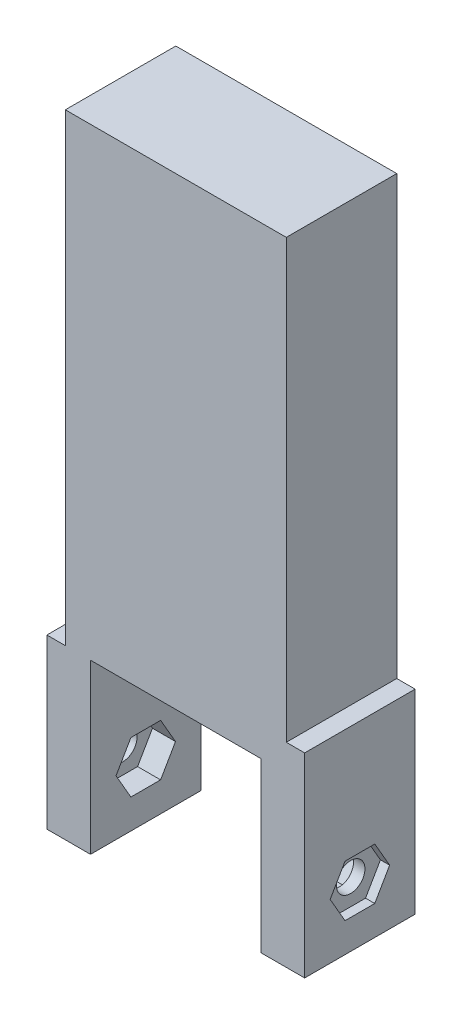
SolidWorks part; units mm, degrees
ref_plane "정면" through (0, 0, 0) normal (0, 0, 1) x (1, 0, 0)
ref_plane "윗면" through (0, 0, 0) normal (0, 1, 0) x (1, 0, 0)
ref_plane "우측면" through (0, 0, 0) normal (1, 0, 0) x (0, 0, -1)
sketch "스케치1" plane through (0, 0, 0) normal (0, 0, 1) x (1, 0, 0)
  line L0 (-11.9944, 44.775) -> (-11.9944, -5.635)
  line L1 (-11.9944, 44.775) -> (12.0056, 44.775)
  line L2 (12.0056, 44.775) -> (12.0056, -2.7271)
  line L3 (9.2615, -23.9032) -> (14.0002, -23.9032)
  line L4 (14.0002, -2.7271) -> (12.0056, -2.7271)
  line L5 (-11.9944, -5.635) -> (-13.9998, -5.635)
  line L9 (0.0056, 44.775) -> (0.0056, -20.9932) construction
  line L10 (9.2615, -5.6371) -> (-9.2611, -5.635)
  line L12 (9.2615, -23.9032) -> (9.2615, -5.6371)
  line L14 (14.0002, -23.9032) -> (14.0002, -2.7271)
  line L15 (-9.2611, -23.9032) -> (-13.9998, -23.9032)
  line L16 (-9.2611, -23.9032) -> (-9.2611, -5.635)
  line L18 (-13.9998, -23.9032) -> (-13.9998, -5.635)
  dimension "D2" = 12
  dimension "D1" = 50.41
extrude "보스-돌출1" add sketch "스케치1" along normal blind 12
ref_plane "평면11" through (12.0056, 0, 0) normal (1, 0, 0) x (0, 0, -1)
ref_plane "평면12" through (12.0056, 0, 0) normal (1, 0, 0) x (0, 0, -1)
ref_plane "평면13" through (0.0056, 0, 0) normal (1, 0, 0) x (0, 0, -1)
ref_plane "평면14" through (14.0002, 0, 0) normal (1, 0, 0) x (0, 0, -1)
sketch "스케치20" plane through (14.0002, 0, 0) normal (1, 0, 0) x (0, 0, -1)
  line L0 (-4.385, -20.7023) -> (-7.615, -20.7023)
  line L1 (-7.615, -20.7023) -> (-9.2284, -17.9005)
  line L2 (-9.2284, -17.9005) -> (-7.6134, -15.1068)
  line L3 (-7.6134, -15.1068) -> (-4.3803, -15.1068)
  line L4 (-4.3803, -15.1068) -> (-2.7684, -17.9059)
  line L5 (-2.7684, -17.9059) -> (-4.385, -20.7023)
  line L6 (-7.615, -20.7023) -> (-4.3803, -15.1068) construction
  line L7 (-7.6134, -15.1068) -> (-4.385, -20.7023) construction
  line L8 (-2.7684, -17.9059) -> (-9.2284, -17.9005) construction
  line L11 (-12, -23.9032) -> (0, -23.9032) construction
  line L13 (0, -23.9032) -> (0, -2.7271) construction
  point P0 (-6, -17.9032)
  dimension "D1" = 3.2332
  dimension "D2" = 3.2332
  dimension "D3" = 3.23
  dimension "D4" = 3.23
  dimension "D5" = 3.2268
  dimension "D6" = 3.23
  dimension "D7" = 6
  dimension "D8" = 6
extrude "컷-돌출12" cut sketch "스케치20" against normal blind 1
ref_plane "평면15" through (-13.9998, 0, 0) normal (-1, 0, 0) x (0, 0, 1)
sketch "스케치21" plane through (-13.9998, 0, 0) normal (-1, 0, 0) x (0, 0, 1)
  line L0 (7.611, -20.705) -> (4.381, -20.705)
  line L1 (4.381, -20.705) -> (2.7676, -17.9032)
  line L2 (2.7676, -17.9032) -> (4.3826, -15.1096)
  line L3 (4.3826, -15.1096) -> (7.6158, -15.1096)
  line L4 (7.6158, -15.1096) -> (9.2276, -17.9087)
  line L5 (9.2276, -17.9087) -> (7.611, -20.705)
  line L6 (4.381, -20.705) -> (7.6158, -15.1096) construction
  line L7 (4.3826, -15.1096) -> (7.611, -20.705) construction
  line L8 (9.2276, -17.9087) -> (2.7676, -17.9032) construction
  line L11 (12, -5.635) -> (12, -23.9032) construction
  line L13 (12, -23.9032) -> (0, -23.9032) construction
  point P0 (6, -17.9046)
  dimension "D1" = 3.2332
  dimension "D2" = 3.23
  dimension "D3" = 3.2332
  dimension "D4" = 3.23
  dimension "D5" = 3.2268
  dimension "D6" = 3.23
  dimension "D7" = 6
  dimension "D8" = 5.9986
extrude "컷-돌출13" cut sketch "스케치21" against normal blind 1
ref_plane "평면16" through (9.2615, 0, 0) normal (-1, 0, 0) x (0, 0, 1)
sketch "스케치22" plane through (9.2615, 0, 0) normal (-1, 0, 0) x (0, 0, 1)
  line L0 (7.615, -20.7023) -> (4.385, -20.7023)
  line L1 (4.385, -20.7023) -> (2.7716, -17.9005)
  line L2 (2.7716, -17.9005) -> (4.3866, -15.1068)
  line L3 (4.3866, -15.1068) -> (7.6197, -15.1068)
  line L4 (7.6197, -15.1068) -> (9.2316, -17.9059)
  line L5 (9.2316, -17.9059) -> (7.615, -20.7023)
  line L6 (4.385, -20.7023) -> (7.6197, -15.1068) construction
  line L7 (4.3866, -15.1068) -> (7.615, -20.7023) construction
  line L8 (9.2316, -17.9059) -> (2.7716, -17.9005) construction
  line L11 (12, -23.9032) -> (0, -23.9032) construction
  line L12 (12, -5.635) -> (12, -23.9032) construction
  point P0 (6, -17.9032)
  dimension "D1" = 3.2332
  dimension "D2" = 3.2332
  dimension "D3" = 3.23
  dimension "D4" = 3.23
  dimension "D5" = 3.2268
  dimension "D6" = 3.23
  dimension "D7" = 6
  dimension "D8" = 6
extrude "컷-돌출14" cut sketch "스케치22" against normal blind 2.5
ref_plane "평면17" through (-9.2611, 0, 0) normal (1, 0, 0) x (0, 0, -1)
sketch "스케치25" plane through (-9.2611, 0, 0) normal (1, 0, 0) x (0, 0, -1)
  line L0 (-4.385, -20.7023) -> (-7.615, -20.7023)
  line L1 (-7.615, -20.7023) -> (-9.2284, -17.9005)
  line L2 (-9.2284, -17.9005) -> (-7.6134, -15.1068)
  line L3 (-7.6134, -15.1068) -> (-4.3803, -15.1068)
  line L4 (-4.3803, -15.1068) -> (-2.7684, -17.9059)
  line L5 (-2.7684, -17.9059) -> (-4.385, -20.7023)
  line L6 (-7.615, -20.7023) -> (-4.3803, -15.1068) construction
  line L7 (-7.6134, -15.1068) -> (-4.385, -20.7023) construction
  line L8 (-2.7684, -17.9059) -> (-9.2284, -17.9005) construction
  line L9 (0, -23.9032) -> (0, -2.7271) construction
  line L12 (-12, -23.9032) -> (0, -23.9032) construction
  point P0 (-6, -17.9032)
  dimension "D1" = 3.2332
  dimension "D2" = 3.2332
  dimension "D3" = 3.23
  dimension "D4" = 3.23
  dimension "D5" = 3.2268
  dimension "D6" = 3.23
  dimension "D7" = 6
  dimension "D8" = 6
extrude "컷-돌출16" cut sketch "스케치25" against normal blind 2.5
ref_plane "평면18" through (-12.9998, 0, 0) normal (-1, 0, 0) x (0, 0, 1)
sketch "스케치26" plane through (-12.9998, 0, 0) normal (-1, 0, 0) x (0, 0, 1)
  line L0 (12, -23.9032) -> (0, -23.9032) construction
  line L1 (0, -5.635) -> (0, -23.9032) construction
  circle A0 centre (6, -17.9032) radius 1.55
  dimension "D3" = 3.1
  dimension "D1" = 6
  dimension "D2" = 6
extrude "컷-돌출17" cut sketch "스케치26" against normal through all
